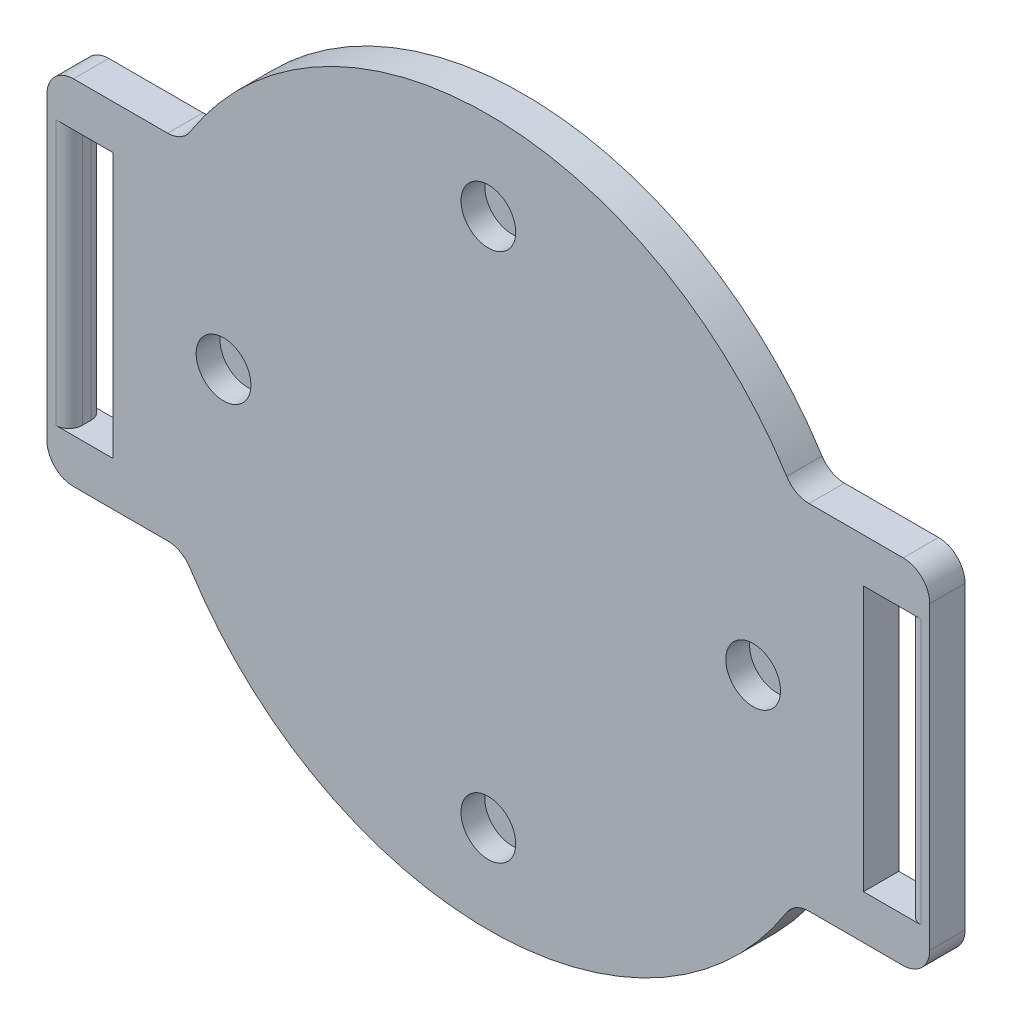
SolidWorks part; units mm, degrees
ref_plane "Plan de face" through (0, 0, 0) normal (0, 0, 1) x (1, 0, 0)
ref_plane "Plan de dessus" through (0, 0, 0) normal (0, 1, 0) x (1, 0, 0)
ref_plane "Plan de droite" through (0, 0, 0) normal (1, 0, 0) x (0, 0, -1)
sketch "Esquisse1" plane through (0, 0, 0) normal (0, 0, 1) x (1, 0, 0)
  line L0 (-34.641, -20) -> (-50, -20)
  line L1 (50, -20) -> (34.641, -20)
  line L2 (50, -20) -> (50, 20)
  line L3 (50, 20) -> (34.641, 20)
  line L4 (-50, -20) -> (-50, 20)
  line L5 (50, -20) -> (-50, 20) construction
  line L6 (50, 20) -> (-50, -20) construction
  line L7 (-34.641, 20) -> (-50, 20)
  arc A0 (-34.641, -20) -> (34.641, -20) centre (0, 0) ccw
  arc A1 (34.641, 20) -> (-34.641, 20) centre (0, 0) ccw
  dimension "D1" = 40
  dimension "D3" = 40
  dimension "D2" = 100
extrude "Boss.-Extru.1" add sketch "Esquisse1" along normal blind 4
sketch "Esquisse2" plane through (0, 0, 4) normal (0, 0, 1) x (1, 0, 0)
  circle A0 centre (0, 0) radius 30 construction
  circle A1 centre (0, 30) radius 3.1
  circle A2 centre (30, 0) radius 3.1
  circle A3 centre (0, -30) radius 3.1
  circle A4 centre (-30, 0) radius 3.1
extrude "Enlèv. mat.-Extru.1" cut sketch "Esquisse2" against normal blind 2.7 and the other way through all
sketch "Esquisse3" plane through (0, 0, 4) normal (0, 0, 1) x (1, 0, 0)
  line L0 (-45, 20) -> (-45, -20) construction
  line L3 (0, 0) -> (0, 42.061) construction
  line L4 (-47.5, -15) -> (-42.5, -15)
  line L5 (-47.5, -15) -> (-47.5, 15)
  line L6 (-47.5, 15) -> (-42.5, 15)
  line L7 (-42.5, -15) -> (-42.5, 15)
  line L8 (-47.5, -15) -> (-42.5, 15) construction
  line L9 (-47.5, 15) -> (-42.5, -15) construction
  line L10 (47.5, 15) -> (42.5, 15)
  line L11 (42.5, -15) -> (42.5, 15)
  line L12 (47.5, -15) -> (42.5, -15)
  line L13 (47.5, -15) -> (47.5, 15)
  line L14 (-50, 20) -> (-50, -20) construction
  point P6 (-45, 0)
  dimension "D1" = 30
  dimension "D2" = 5
  dimension "D3" = 5
extrude "Enlèv. mat.-Extru.2" cut sketch "Esquisse3" against normal blind 12.7
fillet "Congé1" radius 1.5 4 edges at (-47.5, 0, 4) (-47.5, 0, 0) (47.5, 0, 0) (47.5, 0, 4)
fillet "Congé2" radius 3 4 edges at (50, 20, 2) (50, -20, 2) (-50, -20, 2) (-50, 20, 2)
fillet "Congé3" radius 3 4 edges at (-34.641, -20, 2) (34.641, -20, 2) (34.641, 20, 2) (-34.641, 20, 2)
